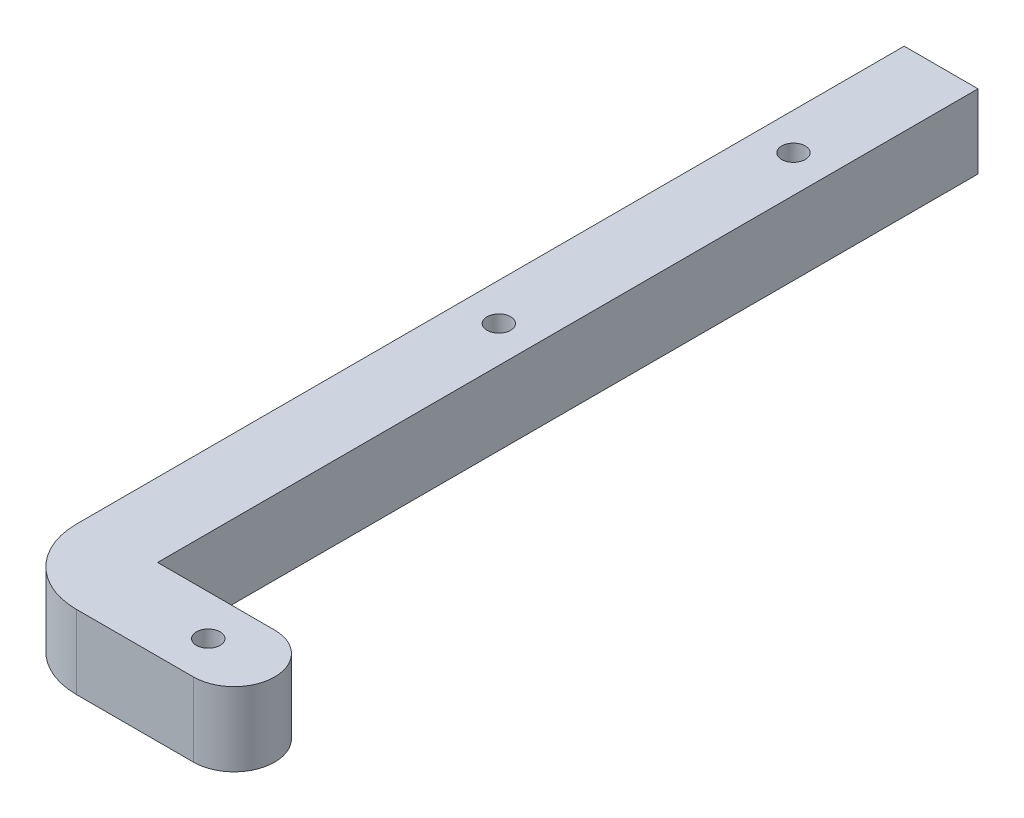
SolidWorks part; units mm, degrees
ref_plane "Front Plane" through (0, 0, 0) normal (0, 0, 1) x (1, 0, 0)
ref_plane "Top Plane" through (0, 0, 0) normal (0, 1, 0) x (1, 0, 0)
ref_plane "Right Plane" through (0, 0, 0) normal (1, 0, 0) x (0, 0, -1)
sketch "Sketch1" plane through (0, 0, 0) normal (0, 1, 0) x (1, 0, 0)
  line L7 (-74.0051, -12.2859) -> (-32.2756, -12.2859) construction
  line L8 (-58.1404, 104.3673) -> (-48.1404, 104.3673)
  line L9 (-58.1404, 104.3673) -> (-58.1404, -6.7859)
  line L11 (-48.1404, 104.3673) -> (-48.1404, -6.7859)
  line L13 (-58.1404, -17.7859) -> (-32.2756, -17.7859)
  line L14 (-58.1404, -6.7859) -> (-58.1404, -17.7859)
  line L15 (-48.1404, -6.7859) -> (-32.2756, -6.7859)
  arc A1 (-32.2756, -17.7859) -> (-32.2756, -6.7859) centre (-32.2756, -12.2859) ccw
  point P7 (-53.1404, -12.303)
  dimension "D1" = 11
  dimension "D2" = 10
extrude "Boss-Extrude1" add sketch "Sketch1" along normal blind 10
fillet "Fillet1" radius 10 1 edges at (-58.1404, 5, 17.7859)
hole_wizard "M3 Clearance Hole1" positions "3DSketch1" profile "Sketch3" hole size "M3" standard "ANSI Metric" end condition through all
sketch3d "3DSketch1"
  line L0 (-32.2756, 0, 6.7859) -> (-48.1404, 0, 6.7859) construction
  line L1 (-35.7756, 0, 12.2859) -> (-26.7756, 0, 12.2859) construction
  line L3 (-58.1404, 0, -104.3673) -> (-58.1404, 0, 7.7859) construction
  line L4 (-48.1404, 0, -104.3673) -> (-58.1404, 0, -104.3673) construction
  arc A0 (-32.2756, 0, 17.7859) -> (-32.2756, 0, 6.7859) centre (-32.2756, 0, 12.2859) ccw construction
  point P0 (-35.7756, 0, 12.2859)
  point P2 (-53.1404, 0, -84.3673)
  point P4 (-53.0597, 0, -44.3674)
  point P11 (-32.2756, 5.5, 12.2859)
  dimension "D2" = 9
  dimension "D1" = 5.5
  dimension "D3" = 5
  dimension "D4" = 20
  dimension "D5" = 40
sketch "Sketch3" plane through (-35.7756, 0, 12.2859) normal (1, 0, 0) x (0, 0, -1)
  line L0 (0, 0) -> (0, 10)
  line L1 (0, 10) -> (1.6, 10)
  line L2 (1.6, 10) -> (1.6, 0)
  line L5 (1.6, 0) -> (0, 0)
  line L11 (0, -6.35) -> (0, 107.95) construction
  dimension "Thru Hole Dia." = 3.2
  dimension "Thru Hole Depth" = 10
